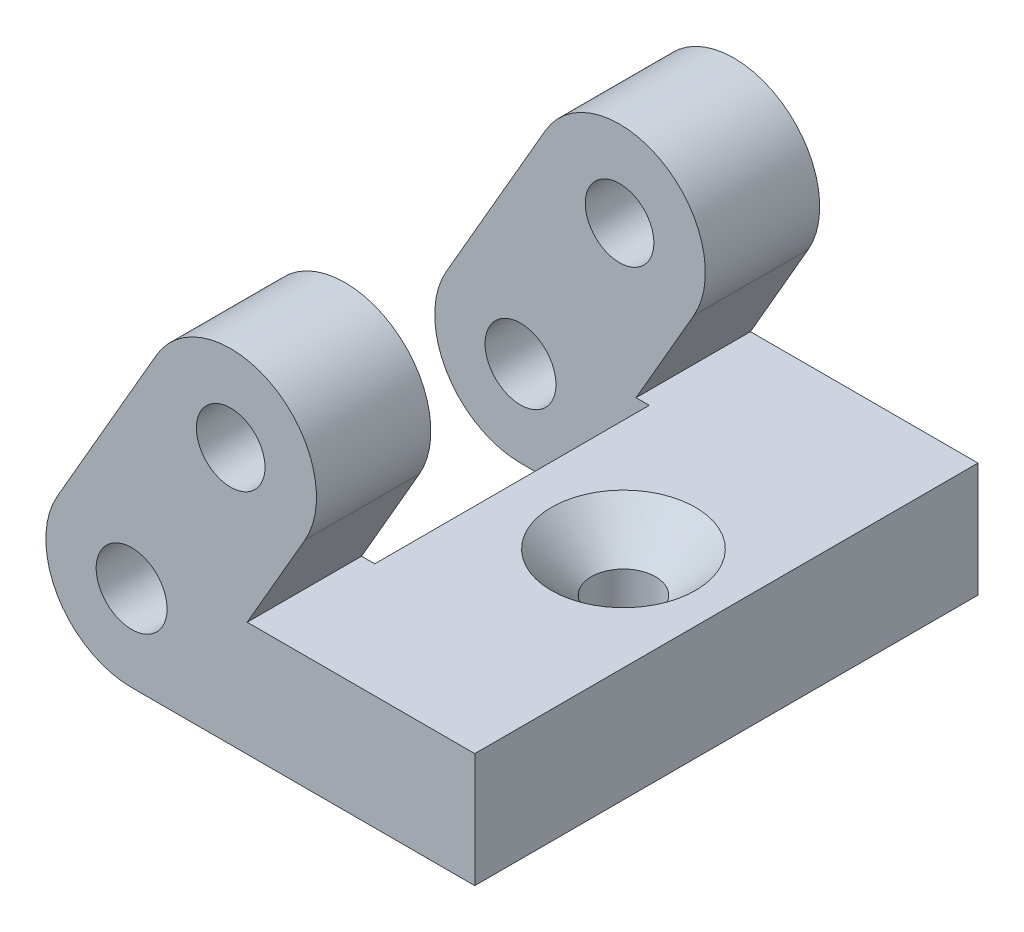
SolidWorks part; units mm, degrees
material "ABS"
ref_plane "Front Plane" through (0, 0, 0) normal (0, 0, 1) x (1, 0, 0)
ref_plane "Top Plane" through (0, 0, 0) normal (0, 1, 0) x (1, 0, 0)
ref_plane "Right Plane" through (0, 0, 0) normal (1, 0, 0) x (0, 0, -1)
sketch "Sketch1" plane through (0, 0, 0) normal (0, 0, 1) x (1, 0, 0)
  line L0 (4.3301, 7.5) -> (0, 0) construction
  line L1 (1.0825, 9.375) -> (-3.2476, 1.875)
  line L2 (0, -3.75) -> (15, -3.75)
  line L3 (15, -3.75) -> (15, 1.25)
  line L4 (15, 1.25) -> (5.0518, 1.25)
  line L5 (5.0518, 1.25) -> (7.5777, 5.625)
  line L6 (0, 0) -> (4.7493, 0) construction
  circle A0 centre (0, 0) radius 1.55
  circle A1 centre (4.3301, 7.5) radius 1.5
  arc A2 (1.0825, 9.375) -> (7.5777, 5.625) centre (4.3301, 7.5) cw
  arc A3 (-3.2476, 1.875) -> (0, -3.75) centre (0, 0) ccw
  dimension "D1" = 3.1
  dimension "D2" = 3
  dimension "D3" = 7.5
  dimension "D4" = 7.5
  dimension "D5" = 5
  dimension "D6" = 15
  dimension "D7" = 60
extrude "Boss-Extrude1" add sketch "Sketch1" against normal mid plane 22
sketch "Sketch5" plane through (0, 0, 0) normal (0, 0, 1) x (1, 0, 0)
  line L0 (-3.6806, 2.125) -> (5.9986, 18.8899)
  line L1 (5.9986, 18.8899) -> (13.3598, 14.6399)
  line L2 (13.3598, 14.6399) -> (3.6806, -2.125)
  line L3 (1.0825, 9.375) -> (-3.2476, 1.875) construction
  arc A0 (-3.6806, 2.125) -> (3.6806, -2.125) centre (0, 0) ccw
  dimension "D1" = 8.5
extrude "Cut-Extrude1" cut sketch "Sketch5" against normal mid plane 12
hole_wizard "CSK for M3 Flat Head Machine Screw1" positions "Sketch4" profile "Sketch3" countersink size "M3" standard "ANSI Metric"
sketch "Sketch4" plane through (0, 1.25, 0) normal (0, 1, 0) x (1, 0, 0)
  point P0 (10.5, 0)
  dimension "D1" = 10.5
sketch "Sketch3" plane through (10.5, 1.25, 0) normal (1, 0, 0) x (0, 0, 1)
  line L0 (0, 0) -> (0, 10.8412)
  line L1 (0, 10.8412) -> (1.4, 10)
  line L2 (1.4, 10) -> (1.4, 1.75)
  line L3 (1.4, 1.75) -> (3.15, 0)
  line L5 (3.15, 0) -> (0, 0)
  line L6 (-1.4, 1.75) -> (-3.15, 0) construction
  line L10 (0, 10.8412) -> (-1.4, 10) construction
  line L11 (0, -6.35) -> (0, 107.95) construction
  dimension "Hole Dia." = 2.8
  dimension "Hole Depth" = 10
  dimension "Near C'Sink Dia." = 6.3
  dimension "Near C'Sink Angle" = 90
  dimension "Drill Angle" = 118
fillet "Fillet1" radius 1 1 edges at (2, -3.75, 0)
